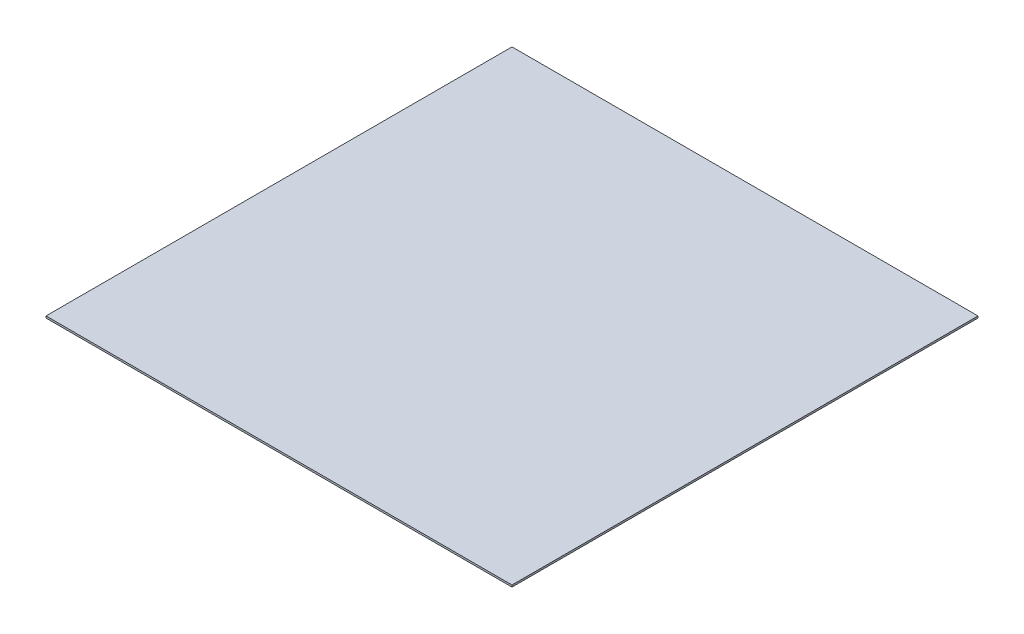
SolidWorks part; units mm, degrees
ref_plane "Front Plane" through (0, 0, 0) normal (0, 0, 1) x (1, 0, 0)
ref_plane "Top Plane" through (0, 0, 0) normal (0, 1, 0) x (1, 0, 0)
ref_plane "Right Plane" through (0, 0, 0) normal (1, 0, 0) x (0, 0, -1)
sketch "Sketch1" plane through (0, 0, 0) normal (0, 1, 0) x (1, 0, 0)
  line L1 (-2500, 2500) -> (2500, 2500)
  line L2 (-2500, 2500) -> (-2500, -2500)
  line L3 (-2500, -2500) -> (2500, -2500)
  line L4 (2500, 2500) -> (2500, -2500)
  line L5 (-2500, 2500) -> (2500, -2500) construction
  line L6 (-2500, -2500) -> (2500, 2500) construction
  point P0 (0, 0)
  dimension "D1" = 5000
  dimension "D2" = 5000
extrude "Boss-Extrude1" add sketch "Sketch1" along normal blind 20
